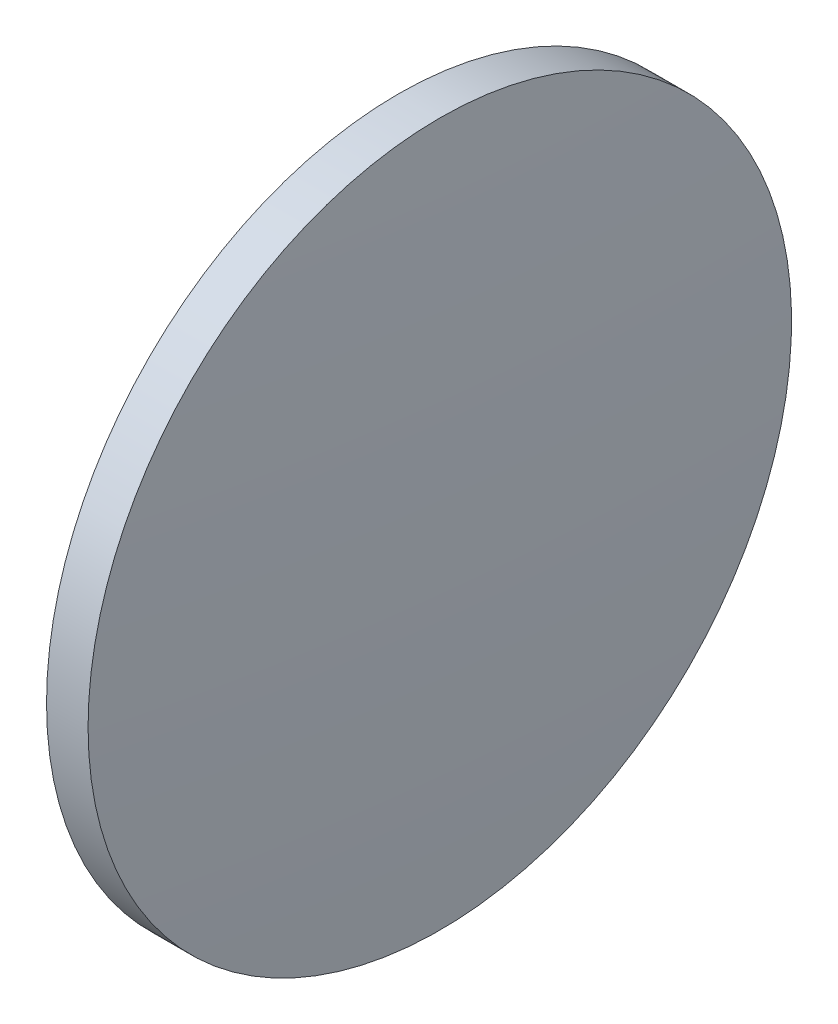
SolidWorks part; units mm, degrees
ref_plane "前视基准面" through (0, 0, 0) normal (0, 0, 1) x (1, 0, 0)
ref_plane "上视基准面" through (0, 0, 0) normal (0, 1, 0) x (1, 0, 0)
ref_plane "右视基准面" through (0, 0, 0) normal (1, 0, 0) x (0, 0, -1)
sketch "草图1" plane through (0, 0, 0) normal (0, 0, 1) x (1, 0, 0)
  line L0 (165.7441, 97.2322) -> (179.7312, 97.2322) construction
  line L1 (171.4164, 122.6322) -> (174.4164, 122.6322)
  line L2 (174.4164, 122.6322) -> (174.4164, 71.8322)
  line L3 (174.4164, 71.8322) -> (171.4164, 71.8322)
  line L4 (171.4164, 71.8322) -> (171.4164, 122.6322)
  arc A0 (171.4164, 122.6322) -> (171.4164, 71.8322) centre (631.8839, 97.2322) ccw
  arc A1 (174.4164, 71.8322) -> (174.4164, 122.6322) centre (-286.0512, 97.2322) ccw
  dimension "D1" = 50.8
  dimension "D2" = 3
revolve "旋转1" add sketch "草图1" angle 360 about L0
